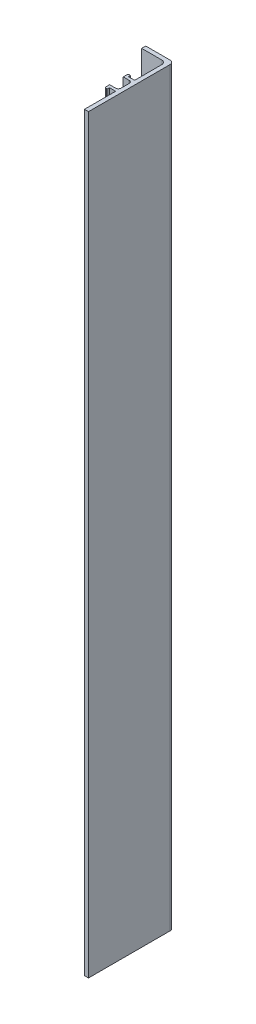
SolidWorks part; units mm, degrees
ref_plane "Alzado" through (0, 0, 0) normal (0, 0, 1) x (1, 0, 0)
ref_plane "Planta" through (0, 0, 0) normal (0, 1, 0) x (1, 0, 0)
ref_plane "Vista lateral" through (0, 0, 0) normal (1, 0, 0) x (0, 0, -1)
sketch "Croquis1" plane through (0, 0, 0) normal (0, 1, 0) x (1, 0, 0)
  line L0 (0, 0) -> (0, 31.5)
  line L1 (0, 31.5) -> (-10.4, 31.5)
  line L2 (-10.4, 31.5) -> (-10.4, 30)
  line L3 (-10.4, 30) -> (-1.5, 30)
  line L4 (-1.5, 30) -> (-1.5, 18.5)
  line L5 (-1.5, 0) -> (0, 0)
  line L6 (-1.5, 18.5) -> (-3.8, 18.5)
  line L7 (-4.7, 19.3) -> (-4.7, 17.5)
  line L8 (-4.7, 17.5) -> (-1.5, 17.5)
  line L9 (-1.5, 12.5) -> (-4.7, 12.5)
  line L11 (-3.8, 11.5) -> (-1.5, 11.5)
  line L12 (-1.5, 11.5) -> (-1.5, 0)
  line L15 (-4.7, 19.3) -> (-3.8, 19.3)
  line L16 (-3.8, 18.5) -> (-3.8, 19.3)
  line L18 (-4.7, 12.5) -> (-4.7, 10.7)
  line L19 (-4.7, 10.7) -> (-3.8, 10.7)
  line L20 (-3.8, 11.5) -> (-3.8, 10.7)
  line L21 (-1.5, 17.5) -> (-1.5, 12.5)
  dimension "D1" = 1.5
  dimension "D2" = 1.5
  dimension "D3" = 8.9
  dimension "D4" = 30
  dimension "D5" = 11.5
  dimension "D6" = 11.5
  dimension "D7" = 3.2
  dimension "D8" = 3.2
  dimension "D9" = 1
  dimension "D10" = 1
  dimension "D11" = 2.3
  dimension "D12" = 0.8
  dimension "D13" = 2.3
  dimension "D14" = 0.8
extrude "Saliente-Extruir1" add sketch "Croquis1" along normal blind 276.5
fillet "Redondeo1" radius 0.5 2 edges at (-4.7, 138.25, -10.7) (-4.7, 138.25, -19.3)
fillet "Redondeo2" radius 1 2 edges at (-1.5, 138.25, -12.5) (-1.5, 138.25, -17.5)
fillet "Redondeo3" radius 1.5 1 edges at (-1.5, 138.25, -30)
fillet "Redondeo4" radius 1.5 1 edges at (0, 138.25, -31.5)
